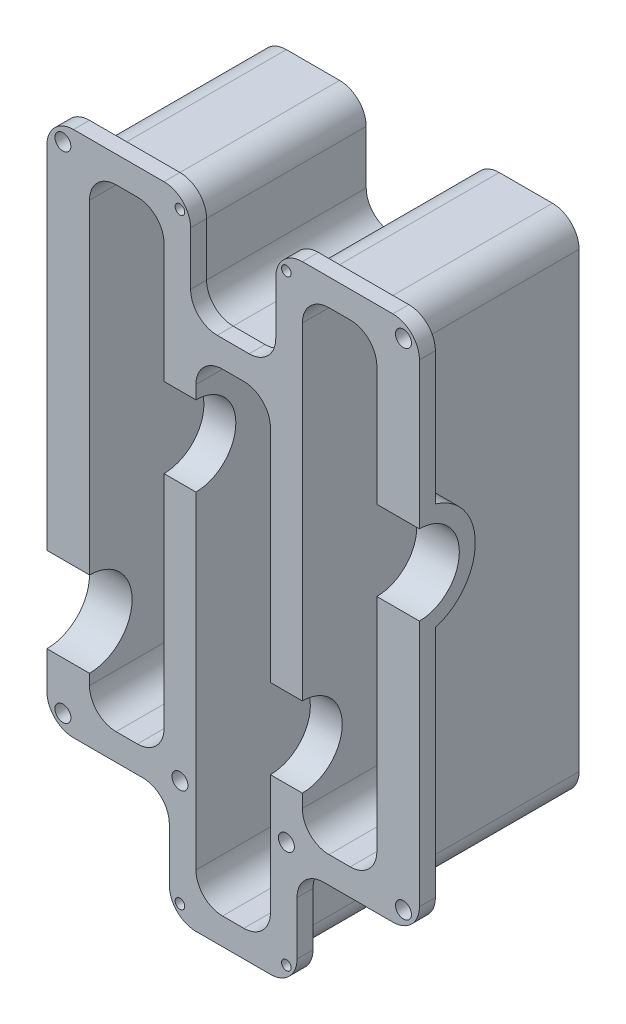
SolidWorks part; units mm, degrees
ref_plane "Front Plane" through (0, 0, 0) normal (0, 0, 1) x (1, 0, 0)
ref_plane "Top Plane" through (0, 0, 0) normal (0, 1, 0) x (1, 0, 0)
ref_plane "Right Plane" through (0, 0, 0) normal (1, 0, 0) x (0, 0, -1)
sketch "Sketch1" plane through (0, 0, 0) normal (0, 0, 1) x (1, 0, 0)
  line L1 (-35, 59.5) -> (35, 59.5)
  line L2 (-35, 59.5) -> (-35, -59.5)
  line L3 (-35, -59.5) -> (35, -59.5)
  line L4 (35, 59.5) -> (35, -59.5)
  line L5 (-35, 59.5) -> (35, -59.5) construction
  line L6 (-35, -59.5) -> (35, 59.5) construction
  point P0 (0, 0)
  dimension "D1" = 119
  dimension "D2" = 70
extrude "Boss-Extrude1" add sketch "Sketch1" along normal blind 35
sketch "Sketch2" plane through (-35, 0, 0) normal (-1, 0, 0) x (0, 0, 1)
  line L0 (35, 59.5) -> (35, -59.5) construction
  line L1 (35, -59.5) -> (0, -59.5) construction
  circle A0 centre (35, -19.5) radius 8
  dimension "D2" = 16
  dimension "D1" = 40
extrude "Cut-Extrude1" cut sketch "Sketch2" against normal blind 8
sketch "Sketch3" plane through (0, 0, 35) normal (0, 0, 1) x (1, 0, 0)
  line L0 (-35, 59.5) -> (-35, -11.5) construction
  line L1 (-27, 54.5) -> (-13, 54.5)
  line L2 (-27, 54.5) -> (-27, -34.5)
  line L3 (-27, -34.5) -> (-13, -34.5)
  line L4 (-13, 54.5) -> (-13, 27)
  line L5 (-7, 34.5) -> (7, 34.5)
  line L6 (-7, 34.5) -> (-7, 27)
  line L7 (-7, -54.5) -> (7, -54.5)
  line L8 (7, 34.5) -> (7, -12)
  line L9 (13, 54.5) -> (27, 54.5)
  line L10 (13, 54.5) -> (13, -12)
  line L11 (13, -34.5) -> (27, -34.5)
  line L12 (27, 54.5) -> (27, -34.5)
  line L13 (-35, -19.5) -> (57.0069, -19.5) construction
  line L14 (-35, -11.5) -> (-35, -27.5) construction
  line L15 (-35, 19.5) -> (53.036, 19.5) construction
  line L16 (-13, 27) -> (-7, 27)
  line L17 (-13, 12) -> (-7, 12)
  line L18 (-13, 12) -> (-13, -34.5)
  line L19 (-7, 12) -> (-7, -54.5)
  line L20 (7, -27) -> (13, -27)
  line L21 (7, -12) -> (13, -12)
  line L22 (7, -27) -> (7, -54.5)
  line L23 (13, -27) -> (13, -34.5)
  line L24 (35, -59.5) -> (35, 59.5) construction
  dimension "D1" = 8
  dimension "D2" = 14
  dimension "D3" = 6
  dimension "D4" = 6
  dimension "D5" = 15
  dimension "D6" = 39
  dimension "D7" = 89
  dimension "D8" = 15
  dimension "D9" = 7.5
  dimension "D10" = 15
  dimension "D11" = 7.5
  dimension "D12" = 15
  dimension "D13" = 89
  dimension "D14" = 8
extrude "Cut-Extrude2" cut sketch "Sketch3" against normal blind 32
sketch "Sketch4" plane through (35, 0, 0) normal (1, 0, 0) x (0, 0, -1)
  line L0 (-35, -59.5) -> (-35, 59.5) construction
  line L1 (-35, -59.5) -> (0, -59.5) construction
  circle A0 centre (-35, 19.5) radius 7.5
  dimension "D2" = 15
  dimension "D1" = 79
extrude "Cut-Extrude3" cut sketch "Sketch4" against normal blind 8
sketch "Sketch5" plane through (0, 0, 35) normal (0, 0, 1) x (1, 0, 0)
  line L0 (35, 59.5) -> (-35, 59.5) construction
  line L1 (-8, 59.5) -> (8, 59.5)
  line L2 (-8, 59.5) -> (-8, 39.5)
  line L3 (-8, 39.5) -> (8, 39.5)
  line L4 (8, 59.5) -> (8, 39.5)
  line L5 (-35, -27.5) -> (-35, -59.5) construction
  line L6 (-35, -39.5) -> (-12, -39.5)
  line L7 (-35, -39.5) -> (-35, -59.5)
  line L8 (-35, -59.5) -> (-12, -59.5)
  line L9 (-12, -39.5) -> (-12, -59.5)
  line L10 (-35, -59.5) -> (35, -59.5) construction
  line L11 (35, -59.5) -> (35, 12) construction
  line L12 (12, -39.5) -> (35, -39.5)
  line L13 (12, -39.5) -> (12, -59.5)
  line L14 (12, -59.5) -> (35, -59.5)
  line L15 (35, -39.5) -> (35, -59.5)
  line L16 (13, -34.5) -> (27, -34.5) construction
  line L17 (7, -54.5) -> (7, -27) construction
  line L18 (-27, -34.5) -> (-13, -34.5) construction
  line L19 (-7, 12) -> (-7, -54.5) construction
  line L20 (-13, 27) -> (-13, 54.5) construction
  line L21 (13, 54.5) -> (13, -12) construction
  line L22 (7, 34.5) -> (-7, 34.5) construction
  dimension "D1" = 5
  dimension "D2" = 5
  dimension "D3" = 5
  dimension "D4" = 5
  dimension "D5" = 5
  dimension "D6" = 5
  dimension "D7" = 5
extrude "Cut-Extrude4" cut sketch "Sketch5" against normal through all
sketch "Sketch6" plane through (-35, 0, 0) normal (-1, 0, 0) x (0, 0, 1)
  line L2 (32, 59.5) -> (0, 59.5)
  line L3 (0, 59.5) -> (0, -39.5)
  line L4 (32, -30.083) -> (32, -39.5)
  line L5 (32, 59.5) -> (32, -8.917)
  line L6 (32, -30.083) -> (32, -39.5)
  line L7 (32, 59.5) -> (32, -8.917)
  line L8 (0, -39.5) -> (32, -39.5)
  arc A2 (32, -8.917) -> (32, -30.083) centre (35, -19.5) ccw
  arc A3 (32, -8.917) -> (32, -30.083) centre (35, -19.5) ccw
  dimension "D1" = 3
extrude "Cut-Extrude5" cut sketch "Sketch6" against normal blind 5
sketch "Sketch7" plane through (0, -39.5, 0) normal (0, -1, 0) x (1, 0, 0)
  line L0 (-12, 0) -> (-30, 0) construction
  line L1 (-30, 32) -> (-12, 32)
  line L2 (-30, 32) -> (-30, 0)
  line L3 (-30, 0) -> (-12, 0)
  line L4 (-12, 32) -> (-12, 0)
  line L5 (-12, 0) -> (-12, 35) construction
extrude "Cut-Extrude6" cut sketch "Sketch7" against normal blind 2
sketch "Sketch8" plane through (-12, 0, 0) normal (-1, 0, 0) x (0, 0, 1)
  line L0 (0, -59.5) -> (0, -37.5) construction
  line L1 (32, -37.5) -> (0, -37.5)
  line L2 (32, -37.5) -> (32, -59.5)
  line L3 (32, -59.5) -> (0, -59.5)
  line L4 (0, -37.5) -> (0, -59.5)
  line L5 (0, -59.5) -> (35, -59.5) construction
extrude "Cut-Extrude7" cut sketch "Sketch8" against normal blind 2
sketch "Sketch9" plane through (0, -59.5, 0) normal (0, -1, 0) x (1, 0, 0)
  line L1 (-10, 32) -> (12, 32)
  line L2 (-10, 32) -> (-10, 0)
  line L3 (-10, 0) -> (12, 0)
  line L4 (12, 32) -> (12, 0)
extrude "Cut-Extrude8" cut sketch "Sketch9" against normal blind 2
sketch "Sketch10" plane through (12, 0, 0) normal (1, 0, 0) x (0, 0, -1)
  line L1 (-32, -57.5) -> (0, -57.5)
  line L2 (-32, -57.5) -> (-32, -39.5)
  line L3 (-32, -39.5) -> (0, -39.5)
  line L4 (0, -57.5) -> (0, -39.5)
extrude "Cut-Extrude9" cut sketch "Sketch10" against normal blind 2
sketch "Sketch11" plane through (0, -39.5, 0) normal (0, -1, 0) x (1, 0, 0)
  line L1 (10, 32) -> (35, 32)
  line L2 (10, 32) -> (10, 0)
  line L3 (10, 0) -> (35, 0)
  line L4 (35, 32) -> (35, 0)
extrude "Cut-Extrude10" cut sketch "Sketch11" against normal blind 2
sketch "Sketch13" plane through (35, 0, 0) normal (1, 0, 0) x (0, 0, -1)
  line L2 (-32, 59.5) -> (0, 59.5)
  line L3 (0, 59.5) -> (0, -37.5)
  line L4 (-32, 29.5623) -> (-32, 59.5)
  line L5 (-32, -39.5) -> (-32, 9.4377)
  line L6 (-32, 29.5623) -> (-32, 59.5)
  line L7 (-32, -37.5) -> (-32, 9.4377)
  line L8 (0, -37.5) -> (-32, -37.5)
  arc A2 (-32, 9.4377) -> (-32, 29.5623) centre (-35, 19.5) ccw
  arc A3 (-32, 9.4377) -> (-32, 29.5623) centre (-35, 19.5) ccw
  dimension "D1" = 3
extrude "Cut-Extrude11" cut sketch "Sketch13" against normal blind 5
sketch "Sketch14" plane through (0, 59.5, 0) normal (0, 1, 0) x (1, 0, 0)
  line L1 (30, -32) -> (8, -32)
  line L2 (30, -32) -> (30, 0)
  line L3 (30, 0) -> (8, 0)
  line L4 (8, -32) -> (8, 0)
extrude "Cut-Extrude12" cut sketch "Sketch14" against normal blind 2
sketch "Sketch16" plane through (8, 0, 0) normal (-1, 0, 0) x (0, 0, 1)
  line L1 (32, 57.5) -> (0, 57.5)
  line L2 (32, 57.5) -> (32, 39.5)
  line L3 (32, 39.5) -> (0, 39.5)
  line L4 (0, 57.5) -> (0, 39.5)
extrude "Cut-Extrude13" cut sketch "Sketch16" against normal blind 2
sketch "Sketch17" plane through (0, 39.5, 0) normal (0, 1, 0) x (1, 0, 0)
  line L1 (10, -32) -> (-8, -32)
  line L2 (10, -32) -> (10, 0)
  line L3 (10, 0) -> (-8, 0)
  line L4 (-8, -32) -> (-8, 0)
extrude "Cut-Extrude14" cut sketch "Sketch17" against normal blind 2
sketch "Sketch18" plane through (-8, 0, 0) normal (1, 0, 0) x (0, 0, -1)
  line L1 (-32, 37.5) -> (0, 37.5)
  line L2 (-32, 37.5) -> (-32, 59.5)
  line L3 (-32, 59.5) -> (0, 59.5)
  line L4 (0, 37.5) -> (0, 59.5)
extrude "Cut-Extrude15" cut sketch "Sketch18" against normal blind 2
sketch "Sketch19" plane through (0, 59.5, 0) normal (0, 1, 0) x (1, 0, 0)
  line L1 (-10, -32) -> (-30, -32)
  line L2 (-10, -32) -> (-10, 0)
  line L3 (-10, 0) -> (-30, 0)
  line L4 (-30, -32) -> (-30, 0)
extrude "Cut-Extrude16" cut sketch "Sketch19" against normal blind 2
fillet "Fillet1" radius 5 12 edges at (-13, -34.5, 19) (-27, -34.5, 19) (13, -34.5, 19) (27, -34.5, 19) (7, -54.5, 19) (-7, -54.5, 19) (27, 54.5, 19) (13, 54.5, 19) (-7, 34.5, 19) (7, 34.5, 19) (-13, 54.5, 19) (-27, 54.5, 19)
fillet "Fillet3" radius 5 12 edges at (-30, 57.5, 16) (-30, -37.5, 16) (-10, -37.5, 16) (-10, -57.5, 16) (10, -57.5, 16) (10, -37.5, 16) (30, 57.5, 16) (10, 57.5, 16) (10, 37.5, 16) (-10, 37.5, 16) (-10, 57.5, 16) (30, -37.5, 16)
fillet "Fillet4" radius 5 12 edges at (12, -39.5, 33.5) (-12, -39.5, 33.5) (-8, 39.5, 33.5) (8, 39.5, 33.5) (35, 59.5, 33.5) (8, 59.5, 33.5) (-8, 59.5, 33.5) (-35, 59.5, 33.5) (-35, -39.5, 33.5) (-12, -59.5, 33.5) (12, -59.5, 33.5) (35, -39.5, 33.5)
sketch "Sketch20" plane through (0, 0, 35) normal (0, 0, 1) x (1, 0, 0)
  line L0 (-13, 59.5) -> (-30, 59.5) construction
  line L1 (-32, 56.5) -> (32, 56.5) construction
  line L2 (-32, 56.5) -> (-32, -36.5) construction
  line L3 (-32, -36.5) -> (32, -36.5) construction
  line L4 (32, 56.5) -> (32, -36.5) construction
  line L6 (-35, 54.5) -> (-35, -11.5) construction
  line L7 (-7, 12) -> (-7, -49.5) construction
  line L8 (7, -49.5) -> (7, -27) construction
  circle A0 centre (-32, 56.5) radius 1.5
  circle A1 centre (32, 56.5) radius 1.5
  circle A2 centre (32, -36.5) radius 1.5
  circle A3 centre (-32, -36.5) radius 1.5
  circle A4 centre (-10, -36.5) radius 1.5
  circle A5 centre (10, -36.5) radius 1.5
  dimension "D7" = 3
  dimension "D1" = 93
  dimension "D2" = 64
  dimension "D3" = 3
  dimension "D4" = 3
  dimension "D5" = 3
  dimension "D6" = 3
extrude "Cut-Extrude17" cut sketch "Sketch20" against normal blind 10
sketch "Sketch21" plane through (0, 0, 35) normal (0, 0, 1) x (1, 0, 0)
  line L0 (-8, 54.5) -> (-8, 44.5) construction
  line L1 (-10, 56.5) -> (10, 56.5) construction
  line L2 (-10, 56.5) -> (-10, -56.5) construction
  line L3 (-10, -56.5) -> (10, -56.5) construction
  line L4 (10, 56.5) -> (10, -56.5) construction
  line L6 (-13, 59.5) -> (-30, 59.5) construction
  circle A0 centre (-10, 56.5) radius 0.9
  circle A1 centre (10, 56.5) radius 0.9
  circle A2 centre (10, -56.5) radius 0.9
  circle A3 centre (-10, -56.5) radius 0.9
  dimension "D5" = 1.8
  dimension "D1" = 113
  dimension "D2" = 20
  dimension "D3" = 2
  dimension "D4" = 3
extrude "Cut-Extrude18" cut sketch "Sketch21" against normal blind 10
sketch "Sketch22" plane through (-13, 0, 0) normal (-1, 0, 0) x (0, 0, 1)
  line L0 (35, 27) -> (3, 27)
  line L1 (3, 27) -> (35, 27) construction
  line L2 (3, 27) -> (3, 12)
  line L3 (3, 12) -> (35, 12) construction
  line L4 (3, 12) -> (35, 12)
  arc A0 (35, 27) -> (35, 12) centre (35, 19.5) ccw
  dimension "D1" = 15
  dimension "D2" = 32
extrude "Boss-Extrude2" add sketch "Sketch22" against normal blind 6
sketch "Sketch24" plane through (7, 0, 0) normal (-1, 0, 0) x (0, 0, 1)
  line L0 (35, -12) -> (3, -12)
  line L1 (3, -12) -> (3, -27)
  line L2 (3, -27) -> (35, -27)
  arc A0 (35, -12) -> (35, -27) centre (35, -19.5) ccw
extrude "Boss-Extrude3" add sketch "Sketch24" against normal blind 6
